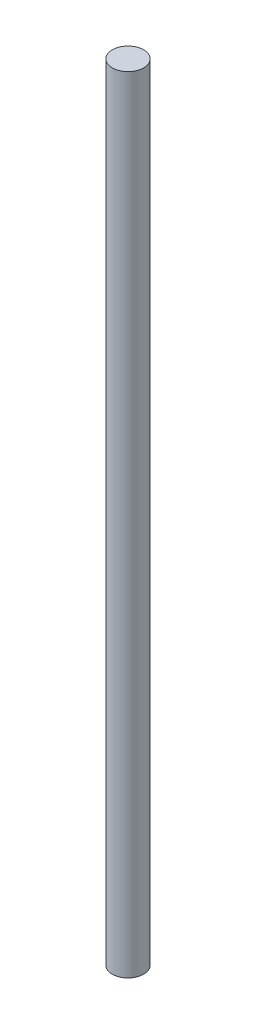
SolidWorks part; units mm, degrees
ref_plane "Alzado" through (0, 0, 0) normal (0, 0, 1) x (1, 0, 0)
ref_plane "Planta" through (0, 0, 0) normal (0, 1, 0) x (1, 0, 0)
ref_plane "Vista lateral" through (0, 0, 0) normal (1, 0, 0) x (0, 0, -1)
sketch "Croquis1" plane through (0, 0, 0) normal (0, 1, 0) x (1, 0, 0)
  circle A0 centre (0, 0) radius 4
  dimension "D1" = 8
extrude "Saliente-Extruir1" add sketch "Croquis1" along normal blind 200
